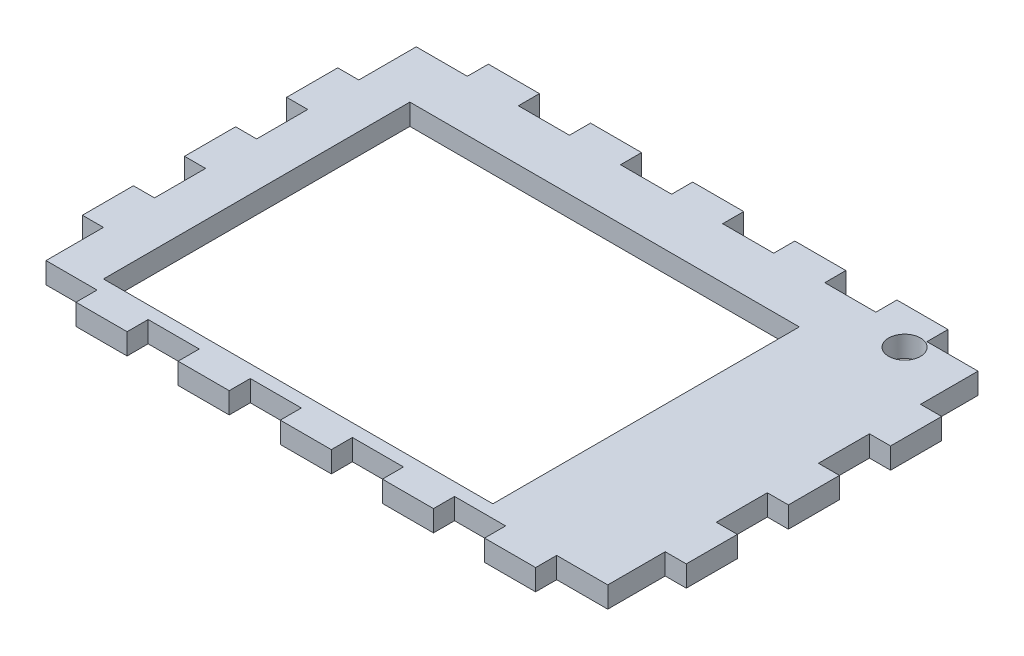
SolidWorks part; units mm, degrees
ref_plane "Plan de face" through (0, 0, 0) normal (0, 0, 1) x (1, 0, 0)
ref_plane "Plan de dessus" through (0, 0, 0) normal (0, 1, 0) x (1, 0, 0)
ref_plane "Plan de droite" through (0, 0, 0) normal (1, 0, 0) x (0, 0, -1)
sketch "Esquisse4" plane through (0, 0, 0) normal (0, 1, 0) x (1, 0, 0)
  line L1 (-44, 29) -> (44, 29)
  line L2 (-44, 29) -> (-44, -29)
  line L3 (-44, -29) -> (44, -29)
  line L4 (44, 29) -> (44, -29)
  line L5 (-44, 29) -> (44, -29) construction
  line L6 (-44, -29) -> (44, 29) construction
  point P0 (0, 0)
  dimension "D1" = 58
  dimension "D2" = 88
extrude "Boss.-Extru.3" add sketch "Esquisse4" along normal blind 3.3
sketch "Esquisse5" plane through (0, 0, 0) normal (0, -1, 0) x (1, 0, 0)
  line L0 (-44, 29) -> (44, 29) construction
  line L1 (4, 29) -> (-4, 29)
  line L2 (4, 29) -> (4, 32.3)
  line L3 (4, 32.3) -> (-4, 32.3)
  line L4 (-4, 29) -> (-4, 32.3)
  point P6 (0, 29)
  point P7 (0, 29)
  dimension "D1" = 3.3
  dimension "D2" = 8
extrude "Boss.-Extru.6" add sketch "Esquisse5" against normal blind 3.3
pattern_linear "Répétition linéaire2" count 3 spacing 16 along (-1, 0, 0) count 3 spacing 16 along (1, 0, 0) of "Boss.-Extru.6"
mirror "Symétrie1" about plane through (0, 0, 0) normal (0, 0, 1) of "Répétition linéaire2", "Boss.-Extru.6"
sketch "Esquisse6" plane through (0, 0, 0) normal (0, -1, 0) x (1, 0, 0)
  line L0 (-44, -29) -> (-44, 29) construction
  line L1 (-47.3, -4) -> (-44, -4)
  line L2 (-47.3, -4) -> (-47.3, 4)
  line L3 (-47.3, 4) -> (-44, 4)
  line L4 (-44, -4) -> (-44, 4)
  point P4 (-44, 0)
  point P7 (-44, 0)
  dimension "D1" = 8
  dimension "D2" = 3.3
extrude "Boss.-Extru.7" add sketch "Esquisse6" against normal blind 3.3
pattern_linear "Répétition linéaire3" count 2 spacing 16 along (0, 0, 1) count 2 spacing 16 along (0, 0, -1) of "Boss.-Extru.7"
mirror "Symétrie2" about plane through (0, 0, 0) normal (1, 0, 0) of "Répétition linéaire3", "Boss.-Extru.7"
sketch "Esquisse7" plane through (0, 0, 0) normal (0, -1, 0) x (1, 0, 0)
  line L0 (-28, 29) -> (-20, 29) construction
  line L1 (-37, 27) -> (24, 27)
  line L2 (-37, 27) -> (-37, -21)
  line L3 (-37, -21) -> (24, -21)
  line L4 (24, 27) -> (24, -21)
  line L5 (-44, 20) -> (-44, 29) construction
  line L7 (44, -20) -> (44, -29) construction
  line L8 (44, -29) -> (36, -29) construction
  circle A0 centre (35, -26.5) radius 2.5
  dimension "D5" = 5
  dimension "D1" = 2
  dimension "D2" = 7
  dimension "D3" = 48
  dimension "D4" = 61
  dimension "D6" = 9
extrude "Enlèv. mat.-Extru.1" cut sketch "Esquisse7" against normal through all both and the other way through all
